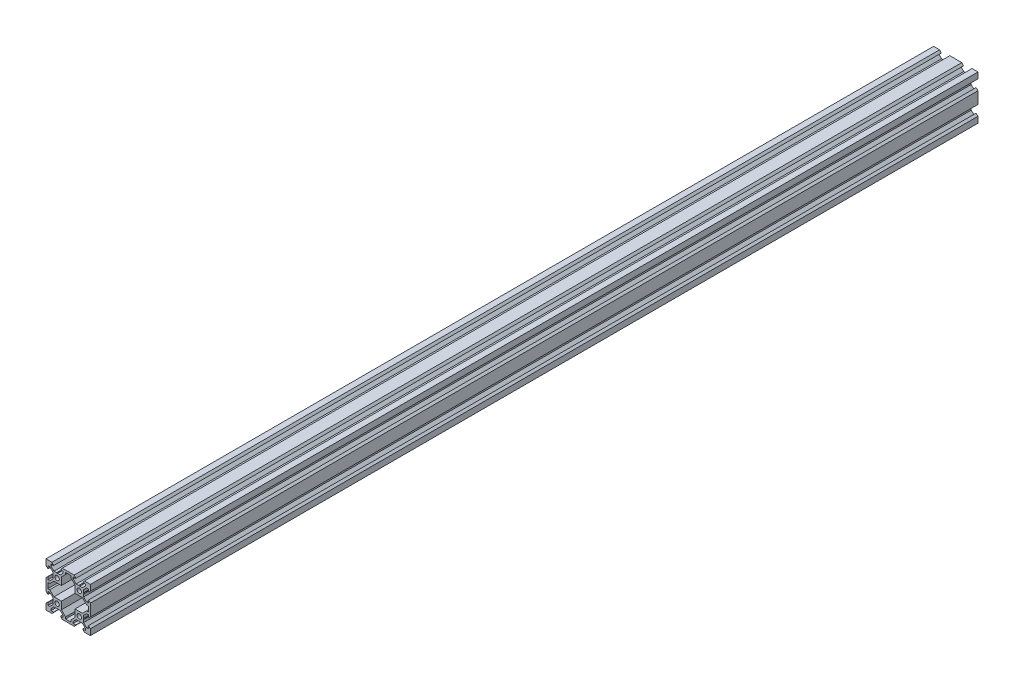
SolidWorks part; units mm, degrees
ref_plane "Front Plane" through (0, 0, 0) normal (0, 0, 1) x (1, 0, 0)
ref_plane "Top Plane" through (0, 0, 0) normal (0, 1, 0) x (1, 0, 0)
ref_plane "Right Plane" through (0, 0, 0) normal (1, 0, 0) x (0, 0, -1)
sketch "Sketch2" plane through (0, 0, 0) normal (0, 0, 1) x (1, 0, 0)
  line L0 (-10, -10) -> (-10.416, -10) construction
  line L1 (-20, -20) -> (20, -20) construction
  line L2 (-20, -20) -> (-20, 20) construction
  line L3 (-20, 20) -> (20, 20) construction
  line L4 (20, -20) -> (20, 20) construction
  line L5 (-20, -20) -> (20, 20) construction
  line L6 (-20, 20) -> (20, -20) construction
  line L7 (0, 0) -> (-20, 0) construction
  line L8 (0, 0) -> (0, -20) construction
  line L9 (0, -20) -> (-20, -20) construction
  line L10 (-20, 20) -> (-20, -20) construction
  line L11 (0, 0) -> (-20, -20) construction
  line L12 (0, -20) -> (-20, 0) construction
  line L14 (-13.9, -12.8393) -> (-13.9, -10.5196)
  line L15 (-12.8393, -6.1) -> (-6.1, -6.1)
  line L16 (-6.1, -12.8393) -> (-6.1, -6.1)
  line L17 (-13.9, -13.9) -> (-6.1, -6.1) construction
  line L18 (-13.9, -6.1) -> (-6.1, -13.9) construction
  line L19 (-13.9, -9.4804) -> (-13.6, -10)
  line L20 (-13.6, -10) -> (-13.9, -10.5196)
  line L21 (-13.9, -9.4804) -> (-13.9, -7.1607)
  line L22 (-12.8393, -13.9) -> (-10.5196, -13.9)
  line L23 (-10, -13.6) -> (-10.5196, -13.9)
  line L24 (-9.4804, -13.9) -> (-10, -13.6)
  line L25 (-9.4804, -13.9) -> (-7.1607, -13.9)
  line L26 (-20, -14.61) -> (-20, -20)
  line L27 (-20, -20) -> (-14.61, -20)
  line L28 (-14.61, -20) -> (-13.0996, -18.2)
  line L29 (-13.0996, -18.2) -> (-15.5, -18.2)
  line L30 (-15.5, -16.5607) -> (-12.8393, -13.9)
  line L31 (-15.5, -18.2) -> (-15.5, -16.5607)
  line L32 (-20, -14.61) -> (-18.2, -13.0996)
  line L33 (-18.2, -13.0996) -> (-18.2, -15.5)
  line L34 (-18.2, -15.5) -> (-16.5607, -15.5)
  line L35 (-16.5607, -15.5) -> (-13.9, -12.8393)
  line L36 (-20, 5.39) -> (-20, -5.39)
  line L37 (-13.9, -13.9) -> (-7.1607, -13.9) construction
  line L38 (-13.9, -13.9) -> (-13.9, -7.1607) construction
  line L39 (-12.8393, -6.1) -> (-6.1, -6.1) construction
  line L40 (-6.1, -12.8393) -> (-6.1, -6.1) construction
  line L41 (-13.9, -13.9) -> (-6.1, -6.1) construction
  line L42 (-13.9, -6.1) -> (-6.1, -13.9) construction
  line L43 (-20, -5.39) -> (-18.2, -6.9004)
  line L44 (-18.2, -6.9004) -> (-18.2, -4.5007)
  line L45 (-18.2, -4.5007) -> (-16.56, -4.5007)
  line L46 (-16.56, -4.5007) -> (-13.9, -7.1607)
  line L47 (-12.8393, -6.1) -> (-16.56, -2.3793)
  line L48 (-16.56, -2.3793) -> (-18.2, -2.3793)
  line L49 (-18.2, -2.3793) -> (-18.2, 2.3793)
  line L50 (-13.9, -7.1607) -> (-13.9, -6.1) construction
  line L51 (-13.9, -7.1607) -> (-13.9, -6.1) construction
  line L52 (-13.9, -6.1) -> (-12.8393, -6.1) construction
  line L53 (-13.9, -6.1) -> (-12.8393, -6.1) construction
  line L54 (-2.3793, -16.56) -> (-2.3793, -18.2)
  line L55 (-20, 0) -> (-20, 20) construction
  line L56 (-2.3793, -18.2) -> (2.3793, -18.2)
  line L57 (5.39, -20) -> (-5.39, -20)
  line L58 (-5.39, -20) -> (-6.9004, -18.2)
  line L59 (-6.9004, -18.2) -> (-4.5007, -18.2)
  line L60 (-4.5007, -18.2) -> (-4.5007, -16.56)
  line L61 (-4.5007, -16.56) -> (-7.1607, -13.9)
  line L62 (-6.1, -12.8393) -> (-2.3793, -16.56)
  line L63 (-6.1, -13.9) -> (-6.1, -12.8393) construction
  line L64 (-6.1, -13.9) -> (-6.1, -12.8393) construction
  line L65 (-7.1607, -13.9) -> (-6.1, -13.9) construction
  line L66 (-7.1607, -13.9) -> (-6.1, -13.9) construction
  line L67 (15.5, -16.5607) -> (12.8393, -13.9)
  line L68 (16.5607, -15.5) -> (13.9, -12.8393)
  line L69 (18.2, -15.5) -> (16.5607, -15.5)
  line L70 (18.2, -13.0996) -> (18.2, -15.5)
  line L71 (20, -14.61) -> (18.2, -13.0996)
  line L72 (20, -14.61) -> (20, -20)
  line L73 (20, -20) -> (14.61, -20)
  line L74 (14.61, -20) -> (13.0996, -18.2)
  line L75 (13.0996, -18.2) -> (15.5, -18.2)
  line L76 (2.3793, -16.56) -> (2.3793, -18.2)
  line L77 (5.39, -20) -> (6.9004, -18.2)
  line L78 (6.9004, -18.2) -> (4.5007, -18.2)
  line L79 (4.5007, -18.2) -> (4.5007, -16.56)
  line L80 (4.5007, -16.56) -> (7.1607, -13.9)
  line L81 (6.1, -12.8393) -> (2.3793, -16.56)
  line L82 (10, -13.6) -> (10.5196, -13.9)
  line L83 (12.8393, -13.9) -> (10.5196, -13.9)
  line L84 (9.4804, -13.9) -> (7.1607, -13.9)
  line L85 (9.4804, -13.9) -> (10, -13.6)
  line L86 (13.9, -9.4804) -> (13.6, -10)
  line L87 (13.6, -10) -> (13.9, -10.5196)
  line L88 (13.9, -12.8393) -> (13.9, -10.5196)
  line L89 (6.1, -12.8393) -> (6.1, -6.1)
  line L90 (13.9, -9.4804) -> (13.9, -7.1607)
  line L91 (12.8393, -6.1) -> (6.1, -6.1)
  line L92 (16.56, -4.5007) -> (13.9, -7.1607)
  line L93 (20, -5.39) -> (18.2, -6.9004)
  line L94 (18.2, -6.9004) -> (18.2, -4.5007)
  line L95 (18.2, -4.5007) -> (16.56, -4.5007)
  line L96 (16.56, -2.3793) -> (18.2, -2.3793)
  line L97 (12.8393, -6.1) -> (16.56, -2.3793)
  line L98 (18.2, -2.3793) -> (18.2, 2.3793)
  line L99 (20, 5.39) -> (20, -5.39)
  line L100 (-7.1607, 13.9) -> (-6.1, 13.9) construction
  line L101 (-7.1607, 13.9) -> (-6.1, 13.9) construction
  line L102 (-6.1, 13.9) -> (-6.1, 12.8393) construction
  line L103 (-6.1, 13.9) -> (-6.1, 12.8393) construction
  line L104 (-13.9, 6.1) -> (-12.8393, 6.1) construction
  line L105 (-13.9, 6.1) -> (-12.8393, 6.1) construction
  line L106 (-13.9, 7.1607) -> (-13.9, 6.1) construction
  line L107 (-13.9, 7.1607) -> (-13.9, 6.1) construction
  line L108 (-13.9, 6.1) -> (-6.1, 13.9) construction
  line L109 (-13.9, 13.9) -> (-6.1, 6.1) construction
  line L110 (-6.1, 12.8393) -> (-6.1, 6.1) construction
  line L111 (-12.8393, 6.1) -> (-6.1, 6.1) construction
  line L112 (-13.9, 13.9) -> (-13.9, 7.1607) construction
  line L113 (-13.9, 13.9) -> (-7.1607, 13.9) construction
  line L114 (-13.9, 6.1) -> (-6.1, 13.9) construction
  line L115 (-13.9, 13.9) -> (-6.1, 6.1) construction
  line L116 (0, 0) -> (-20, 20) construction
  line L117 (0, 20) -> (-20, 20) construction
  line L118 (-20, 20) -> (20, 20) construction
  line L119 (-10, 10) -> (-10.416, 10) construction
  line L120 (12.8393, 6.1) -> (16.56, 2.3793)
  line L121 (16.56, 2.3793) -> (18.2, 2.3793)
  line L122 (18.2, 4.5007) -> (16.56, 4.5007)
  line L123 (18.2, 6.9004) -> (18.2, 4.5007)
  line L124 (20, 5.39) -> (18.2, 6.9004)
  line L125 (16.56, 4.5007) -> (13.9, 7.1607)
  line L126 (12.8393, 6.1) -> (6.1, 6.1)
  line L127 (13.9, 9.4804) -> (13.9, 7.1607)
  line L128 (6.1, 12.8393) -> (6.1, 6.1)
  line L129 (13.9, 12.8393) -> (13.9, 10.5196)
  line L130 (13.6, 10) -> (13.9, 10.5196)
  line L131 (13.9, 9.4804) -> (13.6, 10)
  line L132 (9.4804, 13.9) -> (10, 13.6)
  line L133 (9.4804, 13.9) -> (7.1607, 13.9)
  line L134 (12.8393, 13.9) -> (10.5196, 13.9)
  line L135 (10, 13.6) -> (10.5196, 13.9)
  line L136 (6.1, 12.8393) -> (2.3793, 16.56)
  line L137 (4.5007, 16.56) -> (7.1607, 13.9)
  line L138 (4.5007, 18.2) -> (4.5007, 16.56)
  line L139 (6.9004, 18.2) -> (4.5007, 18.2)
  line L140 (5.39, 20) -> (6.9004, 18.2)
  line L141 (2.3793, 16.56) -> (2.3793, 18.2)
  line L142 (13.0996, 18.2) -> (15.5, 18.2)
  line L143 (14.61, 20) -> (13.0996, 18.2)
  line L144 (20, 20) -> (14.61, 20)
  line L145 (20, 14.61) -> (20, 20)
  line L146 (20, 14.61) -> (18.2, 13.0996)
  line L147 (18.2, 13.0996) -> (18.2, 15.5)
  line L148 (18.2, 15.5) -> (16.5607, 15.5)
  line L149 (16.5607, 15.5) -> (13.9, 12.8393)
  line L150 (15.5, 16.5607) -> (12.8393, 13.9)
  line L151 (-6.1, 12.8393) -> (-2.3793, 16.56)
  line L152 (-4.5007, 16.56) -> (-7.1607, 13.9)
  line L153 (-4.5007, 18.2) -> (-4.5007, 16.56)
  line L154 (-6.9004, 18.2) -> (-4.5007, 18.2)
  line L155 (-5.39, 20) -> (-6.9004, 18.2)
  line L156 (5.39, 20) -> (-5.39, 20)
  line L157 (-2.3793, 18.2) -> (2.3793, 18.2)
  line L158 (-2.3793, 16.56) -> (-2.3793, 18.2)
  line L159 (-16.56, 2.3793) -> (-18.2, 2.3793)
  line L160 (-12.8393, 6.1) -> (-16.56, 2.3793)
  line L161 (-16.56, 4.5007) -> (-13.9, 7.1607)
  line L162 (-18.2, 4.5007) -> (-16.56, 4.5007)
  line L163 (-18.2, 6.9004) -> (-18.2, 4.5007)
  line L164 (-20, 5.39) -> (-18.2, 6.9004)
  line L165 (-16.5607, 15.5) -> (-13.9, 12.8393)
  line L166 (-18.2, 15.5) -> (-16.5607, 15.5)
  line L167 (-18.2, 13.0996) -> (-18.2, 15.5)
  line L168 (-20, 14.61) -> (-18.2, 13.0996)
  line L169 (-15.5, 18.2) -> (-15.5, 16.5607)
  line L170 (-15.5, 16.5607) -> (-12.8393, 13.9)
  line L171 (-13.0996, 18.2) -> (-15.5, 18.2)
  line L172 (-14.61, 20) -> (-13.0996, 18.2)
  line L173 (-20, 20) -> (-14.61, 20)
  line L174 (-20, 14.61) -> (-20, 20)
  line L175 (-9.4804, 13.9) -> (-7.1607, 13.9)
  line L176 (-9.4804, 13.9) -> (-10, 13.6)
  line L177 (-10, 13.6) -> (-10.5196, 13.9)
  line L178 (-12.8393, 13.9) -> (-10.5196, 13.9)
  line L179 (-13.9, 9.4804) -> (-13.9, 7.1607)
  line L180 (-13.6, 10) -> (-13.9, 10.5196)
  line L181 (-13.9, 9.4804) -> (-13.6, 10)
  line L182 (-6.1, 12.8393) -> (-6.1, 6.1)
  line L183 (-12.8393, 6.1) -> (-6.1, 6.1)
  line L184 (-13.9, 12.8393) -> (-13.9, 10.5196)
  line L185 (15.5, -16.5607) -> (15.5, -18.2)
  line L186 (15.5, 16.5607) -> (15.5, 18.2)
  circle A0 centre (-10, -10) radius 2
  circle A1 centre (10, -10) radius 2
  circle A2 centre (10, 10) radius 2
  circle A3 centre (-10, 10) radius 2
  point P0 (0, 0)
  point P6 (-10, -10)
  point P70 (0, -18.2)
  point P107 (20, 0)
  point P108 (18.2, 0)
  point P146 (-18.2, 0)
  point P167 (0, 18.2)
  point P168 (-10, 10)
  dimension "D2" = 4
  dimension "D1" = 40
  dimension "D3" = 7.8
  dimension "D4" = 0.3
  dimension "D5" = 120
  dimension "D6" = 0.75
  dimension "D7" = 5.39
  dimension "D8" = 50
  dimension "D9" = 4.5
  dimension "D10" = 1.5104
  dimension "D11" = 1.8
  dimension "D12" = 50
  dimension "D13" = 5.39
  dimension "D14" = 1.5
  dimension "D15" = 2.66
extrude "Boss-Extrude1" add sketch "Sketch2" against normal blind 800
